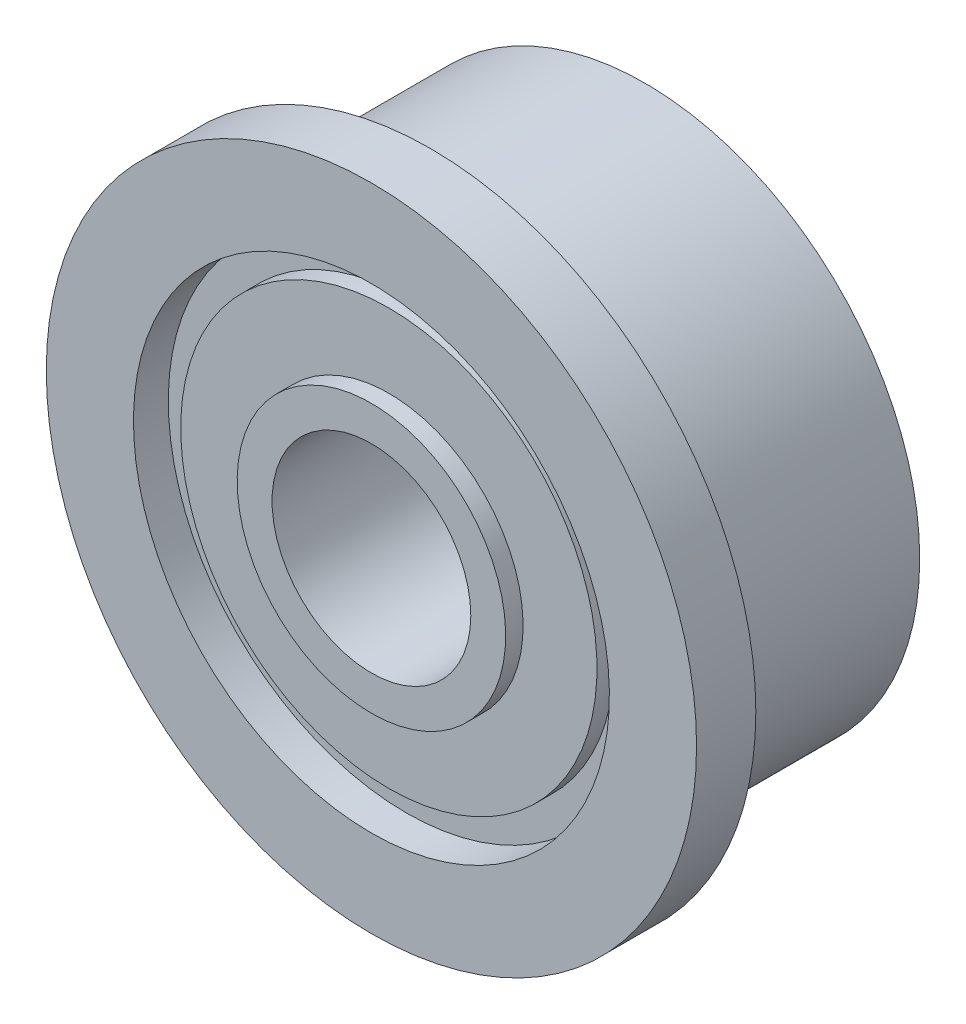
SolidWorks part; units mm, degrees
material "Chrome Stainless Steel"
ref_plane "Front Plane" through (0, 0, 0) normal (0, 0, 1) x (1, 0, 0)
ref_plane "Top Plane" through (0, 0, 0) normal (0, 1, 0) x (1, 0, 0)
ref_plane "Right Plane" through (0, 0, 0) normal (1, 0, 0) x (0, 0, -1)
sketch "Sketch1" plane through (0, 0, 0) normal (1, 0, 0) x (0, 0, -1)
  line L0 (0, 4.7371) -> (0, 0)
  line L1 (0, 4.7371) -> (0.8636, 4.7371)
  line L3 (0, 0) -> (3.9878, 0)
  line L4 (3.9878, 4.0005) -> (3.9878, 0)
  line L5 (3.9878, 4.0005) -> (1.3716, 4.0005)
  line L7 (1.3716, 4.0005) -> (1.3716, 3.7465)
  line L8 (1.3716, 3.7465) -> (0.8636, 3.7465)
  line L9 (0.8636, 3.7465) -> (0.8636, 4.7371)
  dimension "D1" = 4.7371
  dimension "D2" = 0.8636
  dimension "D3" = 3.9878
  dimension "D4" = 4.0005
  dimension "D5" = 0.508
  dimension "D6" = 0.254
revolve "Revolve1" add sketch "Sketch1" angle 360 about L3
sketch "Sketch2" plane through (0, 0, 0) normal (0, 0, 1) x (1, 0, 0)
  circle A0 centre (0, 0) radius 1.4478
  dimension "D1" = 2.8956
extrude "Extrude1" cut sketch "Sketch2" against normal through all
sketch "Sketch3" plane through (0, 0, 0) normal (1, 0, 0) x (0, 0, -1)
  line L0 (0, 0) -> (3.9878, 0) construction
  line L1 (3.9878, -1.4478) -> (3.9878, 1.4478) construction
  line L2 (3.9878, 0) -> (3.9878, 1.9558) construction
  line L3 (3.9878, -4.0005) -> (3.9878, 4.0005) construction
  line L4 (3.9878, 1.9558) -> (3.7338, 1.9558)
  line L5 (3.7338, 1.9558) -> (3.7338, 2.9845)
  line L6 (3.7338, 2.9845) -> (3.9878, 3.4925)
  line L7 (3.9878, 3.4925) -> (3.9878, 1.9558)
  line L8 (3.9878, 1.9558) -> (3.981, 1.9671)
  line L9 (0, 0) -> (0, 1.9558) construction
  line L10 (0, 4.7371) -> (0, -4.7371) construction
  line L11 (0, 1.9558) -> (0.254, 1.9558)
  line L12 (0.254, 1.9558) -> (0.254, 3.0323)
  line L13 (0.254, 3.0323) -> (0.508, 3.0323)
  line L14 (0.508, 3.0323) -> (0.508, 3.4671)
  line L15 (0.508, 3.4671) -> (0, 3.4671)
  line L16 (0, 3.4671) -> (0, 1.9558)
  dimension "D1" = 1.9558
  dimension "D2" = 0.254
  dimension "D3" = 0.508
  dimension "D4" = 3.4925
  dimension "D5" = 3.4671
revolve "Cut-Revolve1" cut sketch "Sketch3" angle 360 about L0
